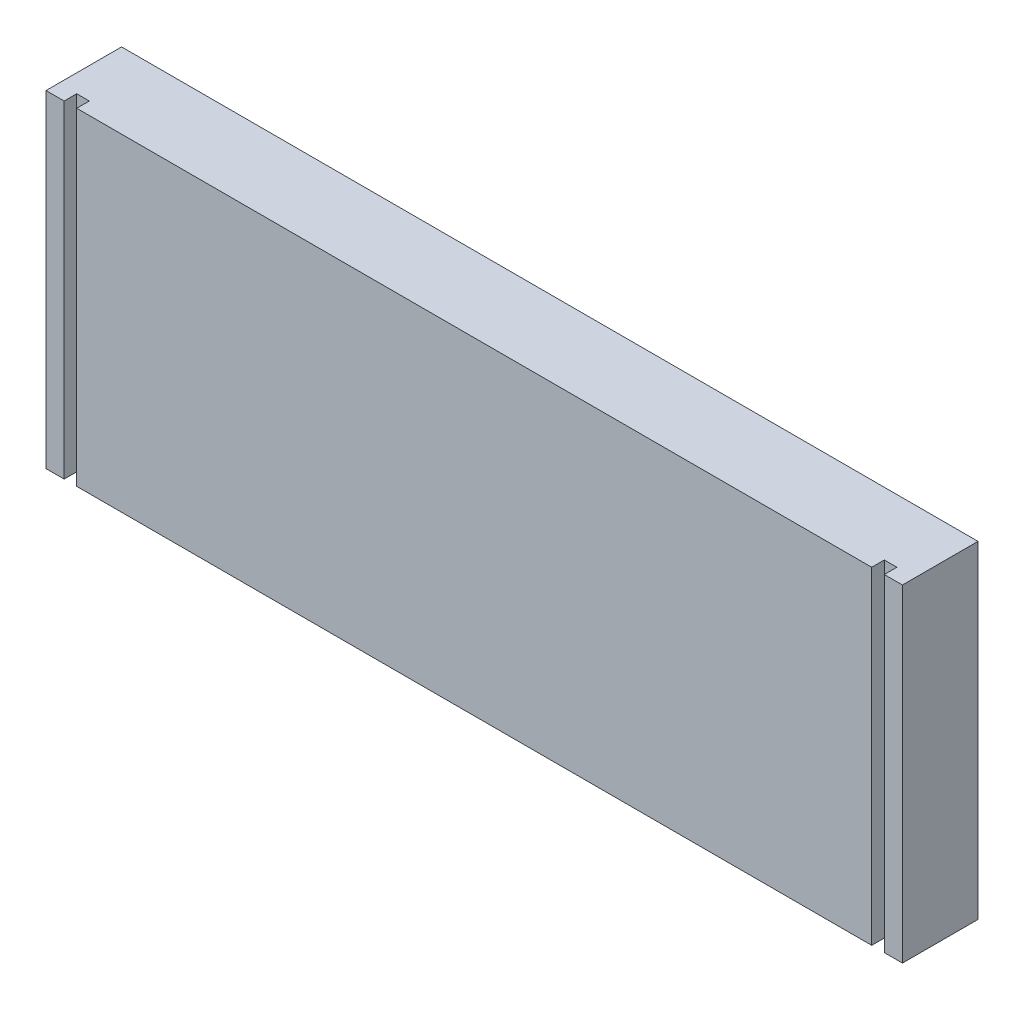
SolidWorks part; units mm, degrees
ref_plane "Front Plane" through (0, 0, 0) normal (0, 0, 1) x (1, 0, 0)
ref_plane "Top Plane" through (0, 0, 0) normal (0, 1, 0) x (1, 0, 0)
ref_plane "Right Plane" through (0, 0, 0) normal (1, 0, 0) x (0, 0, -1)
sketch "Sketch1" plane through (0, 0, 0) normal (0, 0, 1) x (1, 0, 0)
  line L1 (-107.95, -41.275) -> (107.95, -41.275)
  line L2 (-107.95, -41.275) -> (-107.95, 41.275)
  line L3 (-107.95, 41.275) -> (107.95, 41.275)
  line L4 (107.95, -41.275) -> (107.95, 41.275)
  line L5 (-107.95, -41.275) -> (107.95, 41.275) construction
  line L6 (-107.95, 41.275) -> (107.95, -41.275) construction
  point P0 (0, 0)
  dimension "D1" = 215.9
  dimension "D2" = 82.55
extrude "Boss-Extrude2" add sketch "Sketch1" along normal blind 19.05 contours L3 L4 L1 L2
sketch "Sketch3" plane through (0, -41.275, 0) normal (0, -1, 0) x (1, 0, 0)
  line L0 (-107.95, 19.05) -> (107.95, 19.05) construction
  line L2 (-107.95, 19.05) -> (-107.95, 0) construction
  circle A0 centre (-82.55, 9.525) radius 4.7625
  dimension "D1" = 9.525
  dimension "D2" = 9.525
  dimension "D3" = 25.4
extrude "Cut-Extrude1" cut sketch "Sketch3" against normal blind 19.05 contours A0
sketch "Sketch5" plane through (0, -41.275, 0) normal (0, -1, 0) x (1, 0, 0)
  line L0 (-107.95, 19.05) -> (107.95, 19.05) construction
  line L1 (-103.378, 19.05) -> (-100.203, 19.05)
  line L2 (-103.378, 19.05) -> (-103.378, 15.875)
  line L3 (-103.378, 15.875) -> (-100.203, 15.875)
  line L4 (-100.203, 19.05) -> (-100.203, 15.875)
  line L5 (-107.95, 19.05) -> (-107.95, 0) construction
  dimension "D1" = 3.175
  dimension "D2" = 3.175
  dimension "D3" = 4.572
extrude "Cut-Extrude2" cut sketch "Sketch5" against normal through all
mirror "Mirror1" about plane through (0, 0, 0) normal (1, 0, 0) of "Cut-Extrude2", "Cut-Extrude1"
